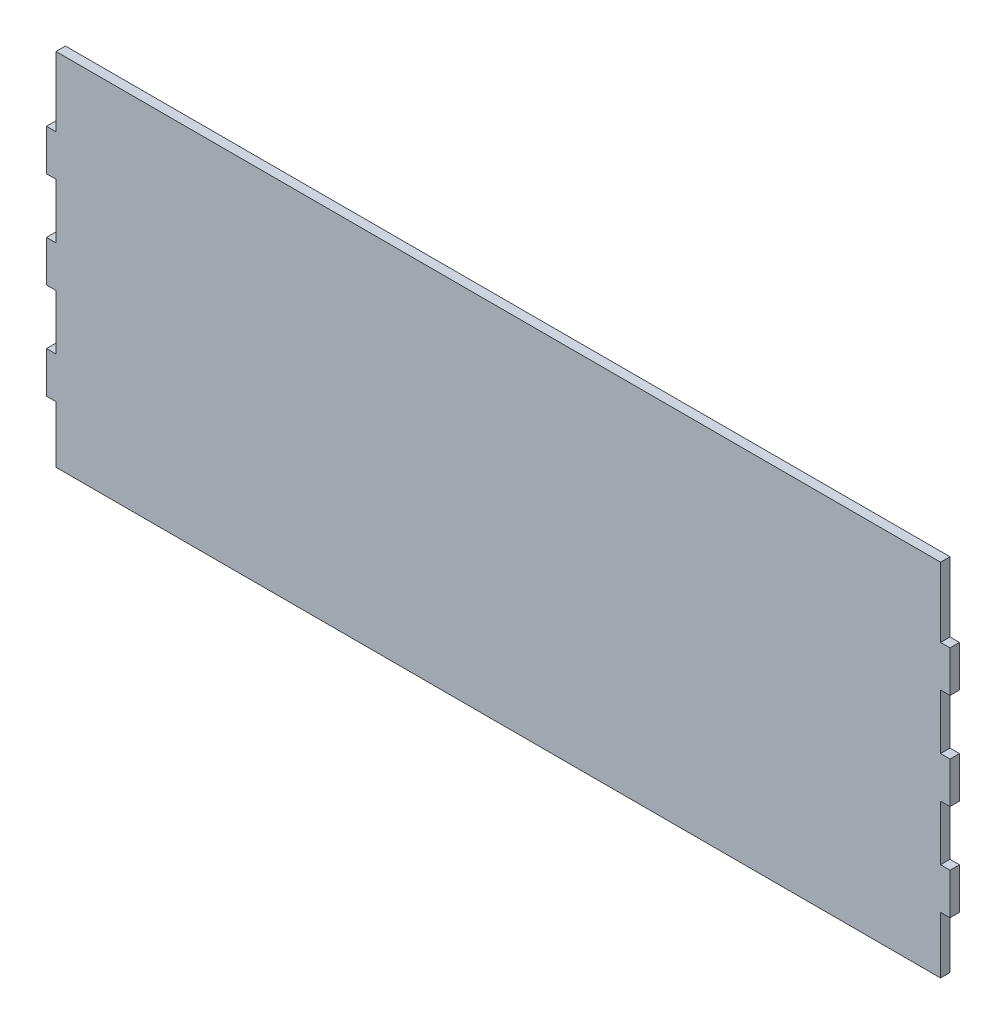
SolidWorks part; units mm, degrees
ref_plane "Front Plane" through (0, 0, 0) normal (0, 0, 1) x (1, 0, 0)
ref_plane "Top Plane" through (0, 0, 0) normal (0, 1, 0) x (1, 0, 0)
ref_plane "Right Plane" through (0, 0, 0) normal (1, 0, 0) x (0, 0, -1)
sketch "Croquis1" plane through (0, 0, 0) normal (0, 0, 1) x (1, 0, 0)
  line L1 (-143.015, 55) -> (143.015, 55)
  line L2 (-143.015, 55) -> (-143.015, -55)
  line L3 (-143.015, -55) -> (143.015, -55)
  line L4 (143.015, 55) -> (143.015, -55)
  line L5 (-143.015, 55) -> (143.015, -55) construction
  line L6 (-143.015, -55) -> (143.015, 55) construction
  point P0 (0, 0)
  dimension "D1" = 286.03
  dimension "D2" = 110
extrude "Saliente-Extruir1" add sketch "Croquis1" along normal blind 3
sketch "Croquis2" plane through (0, 0, 3) normal (0, 0, 1) x (1, 0, 0)
  line L0 (-143.015, 55) -> (-143.015, -55) construction
  line L1 (-143.015, 37) -> (-140.015, 37)
  line L2 (-143.015, 37) -> (-143.015, 23.9518)
  line L3 (-143.015, 23.9518) -> (-140.015, 23.9518)
  line L6 (-143.015, 6.5241) -> (-143.015, -6.5241)
  line L8 (-143.015, 6.5241) -> (-140.015, 6.5241)
  line L10 (-143.015, -6.5241) -> (-140.015, -6.5241)
  line L11 (-143.015, -23.9518) -> (-143.015, -37)
  line L12 (-143.015, -23.9518) -> (-140.015, -23.9518)
  line L14 (-143.015, -37) -> (-140.015, -37)
  line L15 (-143.015, -55) -> (143.015, -55) construction
  line L16 (143.015, 55) -> (-143.015, 55) construction
  line L17 (0, -55) -> (0, 55) construction
  line L18 (143.015, -23.9518) -> (140.015, -23.9518)
  line L19 (-140.015, -52) -> (140.015, -52)
  line L20 (140.015, -52) -> (140.015, 52)
  line L21 (-140.015, 52) -> (-140.015, -52)
  line L22 (140.015, 52) -> (-140.015, 52)
  line L24 (140.015, -52) -> (140.015, -37)
  line L25 (-140.015, 52) -> (-140.015, 37)
  line L28 (143.015, -37) -> (140.015, -37)
  line L29 (143.015, -23.9518) -> (143.015, -37)
  line L30 (143.015, 6.5241) -> (140.015, 6.5241)
  line L32 (143.015, -6.5241) -> (140.015, -6.5241)
  line L33 (143.015, 6.5241) -> (143.015, -6.5241)
  line L34 (143.015, 23.9518) -> (140.015, 23.9518)
  line L36 (143.015, 37) -> (140.015, 37)
  line L37 (143.015, 37) -> (143.015, 23.9518)
  line L38 (-140.015, 23.9518) -> (-140.015, 6.5241)
  line L39 (-140.015, -6.5241) -> (-140.015, -23.9518)
  line L40 (-140.015, -37) -> (-140.015, -52)
  line L41 (140.015, -23.9518) -> (140.015, -6.5241)
  line L42 (140.015, 6.5241) -> (140.015, 23.9518)
  line L43 (140.015, 37) -> (140.015, 52)
  line L44 (-140.015, 52) -> (-140.015, 55)
  line L45 (140.015, 52) -> (140.015, 55)
  line L46 (-140.015, -52) -> (-140.015, -55)
  line L47 (140.015, -52) -> (140.015, -55)
  line L48 (-140.015, -55) -> (140.015, -55)
  line L49 (-140.015, 55) -> (140.015, 55)
  line M3 (143.015, -55) -> (143.015, 55)
  line M4 (143.015, 55) -> (-143.015, 55)
  line M5 (-143.015, 55) -> (-143.015, -55)
  line M6 (-143.015, -55) -> (143.015, -55)
  dimension "D3" = 18
  dimension "D4" = 18
  dimension "D1" = 3
  dimension "D2" = 3
extrude "Cortar-Extruir1" cut sketch "Croquis2" against normal blind 3 contours L25 L44 L1 M4 M5 | L38 L3 L8 M5 | L45 L43 L36 M3 M4 | L42 L30 L34 M3 | L41 L18 L32 M3 | L24 L47 L28 M6 M3 | L39 L10 L12 M5 | L46 L40 L14 M5 M6
sketch "Croquis4" plane through (0, 0, 0) normal (0, 0, -1) x (-1, 0, 0)
  line L6 (140.015, 55) -> (140.015, 37) construction
  line L7 (-140.015, 55) -> (140.015, 55)
  line L8 (-140.015, 55) -> (-140.015, 59)
  line L9 (-140.015, 59) -> (140.015, 59)
  line L10 (140.015, 55) -> (140.015, 59)
  dimension "D1" = 4
extrude "Saliente-Extruir3" add sketch "Croquis4" against normal blind 3
sketch "Croquis6" plane through (0, 0, 0) normal (0, 0, -1) x (-1, 0, 0)
  line L0 (-100.0921, -10.7078) -> (100.0921, -10.7078) construction
  text T0 "ITAM MANTIS" font "Century Gothic" height 25
  point P2 (0, -10.7078)
extrude "Cortar-Extruir4" cut sketch "Croquis6" against normal blind 1.5
